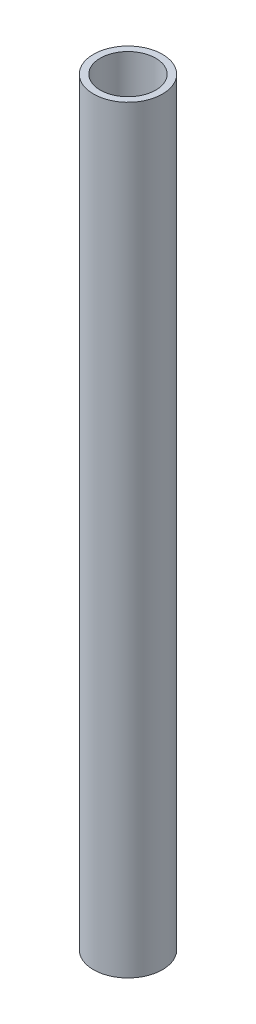
SolidWorks part; units mm, degrees
ref_plane "Front Plane" through (0, 0, 0) normal (0, 0, 1) x (1, 0, 0)
ref_plane "Top Plane" through (0, 0, 0) normal (0, 1, 0) x (1, 0, 0)
ref_plane "Right Plane" through (0, 0, 0) normal (1, 0, 0) x (0, 0, -1)
sketch "Sketch1" plane through (0, 0, 0) normal (0, 1, 0) x (1, 0, 0)
  circle A0 centre (0, 0) radius 5.1054
  circle A1 centre (0, 0) radius 6.35
  dimension "D1" = 12.7
  dimension "D2" = 10.2108
extrude "Boss-Extrude1" add sketch "Sketch1" along normal blind 139.7
